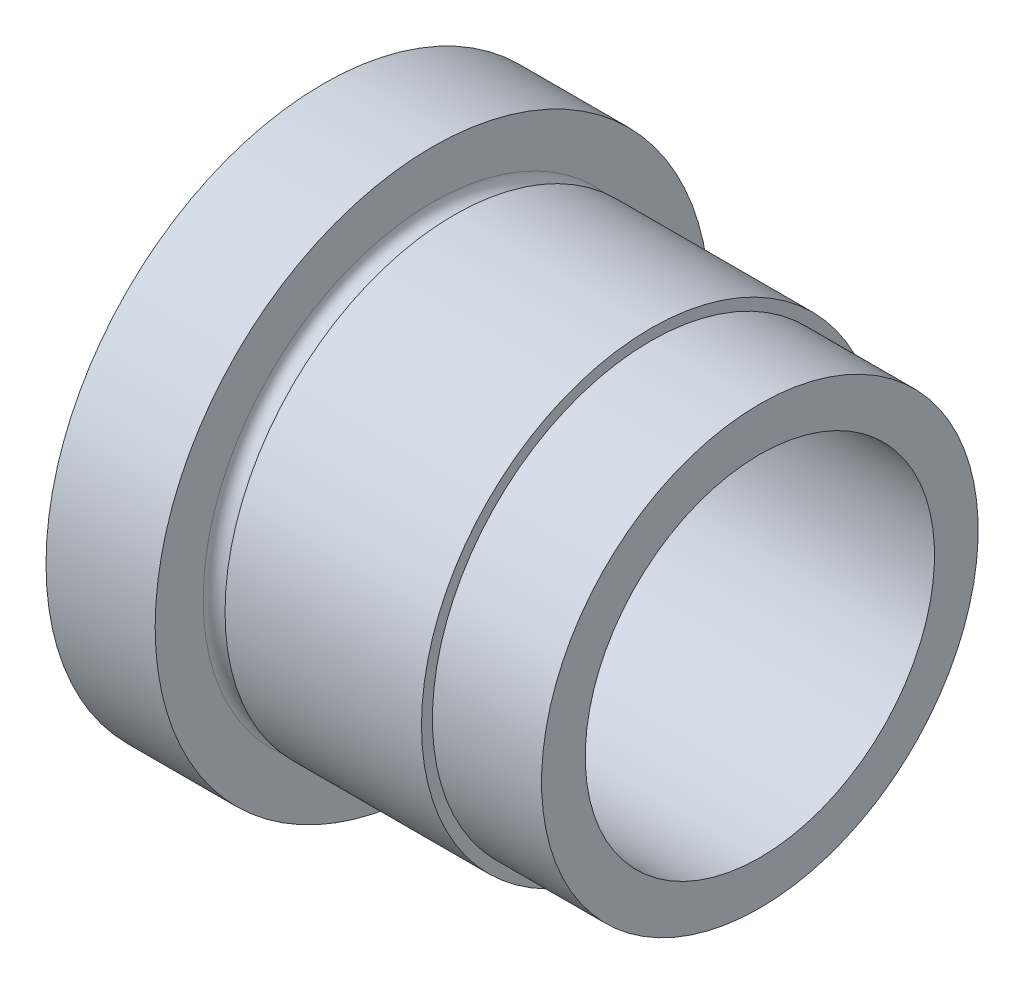
SolidWorks part; units mm, degrees
ref_plane "Plano frontal" through (0, 0, 0) normal (0, 0, 1) x (1, 0, 0)
ref_plane "Plano superior" through (0, 0, 0) normal (0, 1, 0) x (1, 0, 0)
ref_plane "Plano direito" through (0, 0, 0) normal (1, 0, 0) x (0, 0, -1)
sketch "Esboço1" plane through (0, 0, 0) normal (0, 0, 1) x (1, 0, 0)
  line L0 (-138.9253, 0) -> (138.9253, 0) construction
  line L1 (0, 8.05) -> (0, 12.7)
  line L2 (0, 12.7) -> (5, 12.7)
  line L3 (5, 12.7) -> (5, 10.5)
  line L4 (6, 10.5) -> (15, 10.5)
  line L5 (15, 10.5) -> (15, 10)
  line L6 (15, 10) -> (20, 10)
  line L7 (20, 10) -> (20, 8)
  line L8 (20, 8) -> (0.1, 8)
  line L9 (0.1, 8) -> (0.1, 8.05)
  line L10 (0.1, 8.05) -> (0, 8.05)
  line L11 (0, 8.05) -> (0, 0) construction
  arc A0 (5, 10.5) -> (6, 10.5) centre (5.5, 10.5) ccw
  point P3 (0, 0)
  dimension "D8" = 0.5
  dimension "D1" = 16
  dimension "D2" = 16.1
  dimension "D3" = 21
  dimension "D4" = 25.4
  dimension "D5" = 19.9
  dimension "D6" = 5
  dimension "D7" = 20
  dimension "D9" = 5
revolve "Revolução1" add sketch "Esboço1" angle 360 about L0
